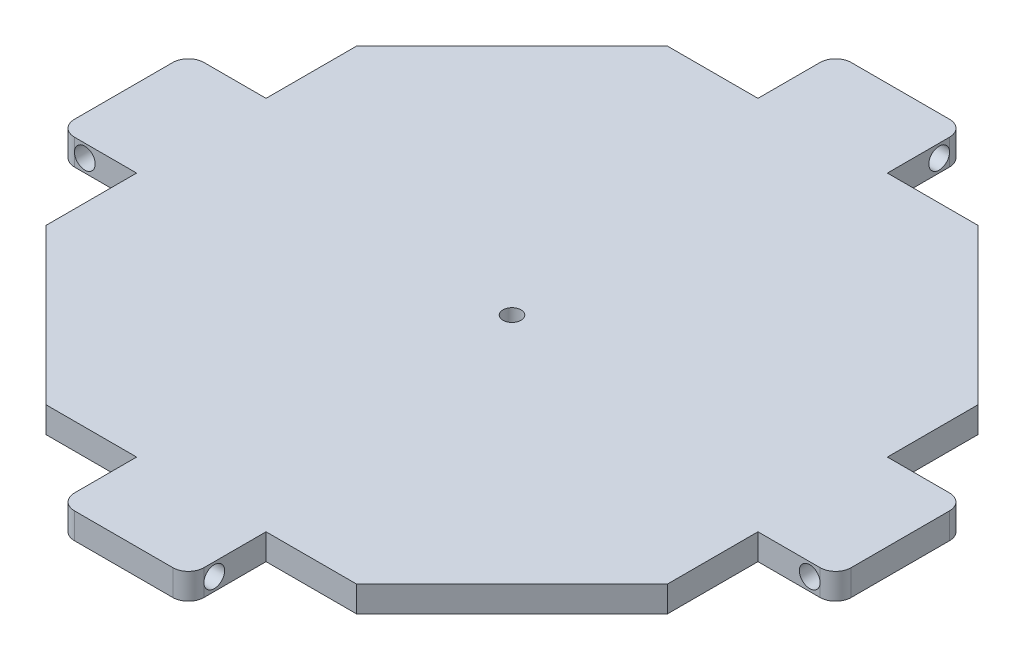
SolidWorks part; units mm, degrees
material "6061 합금"
ref_plane "정면" through (0, 0, 0) normal (0, 0, 1) x (1, 0, 0)
ref_plane "윗면" through (0, 0, 0) normal (0, 1, 0) x (1, 0, 0)
ref_plane "우측면" through (0, 0, 0) normal (1, 0, 0) x (0, 0, -1)
sketch "스케치1" plane through (0, 0, 0) normal (0, 1, 0) x (1, 0, 0)
  line L0 (0, 0) -> (-27.1519, 0) construction
  line L7 (39, 0) -> (-66.3, 0) construction
  line L9 (0, 39) -> (0, -39) construction
  line L14 (-30, -60) -> (30, -60)
  line L15 (30, -60) -> (60, -30)
  line L16 (60, -30) -> (60, 30)
  line L17 (60, 30) -> (30, 60)
  line L18 (30, 60) -> (-30, 60)
  line L19 (-30, 60) -> (-60, 30)
  line L20 (-60, 30) -> (-60, -30)
  line L21 (-60, -30) -> (-30, -60)
  line L22 (-60, 12.5) -> (-75, 12.5)
  line L23 (-75, 12.5) -> (-75, -12.5)
  line L24 (-75, -12.5) -> (-60, -12.5)
  line L25 (-12.5, -60) -> (-12.5, -75)
  line L26 (-12.5, -75) -> (12.5, -75)
  line L27 (12.5, -75) -> (12.5, -60)
  line L28 (60, -12.5) -> (75, -12.5)
  line L29 (75, -12.5) -> (75, 12.5)
  line L30 (75, 12.5) -> (60, 12.5)
  line L31 (-12.5, 60) -> (-12.5, 75)
  line L32 (-12.5, 75) -> (12.5, 75)
  line L33 (12.5, 75) -> (12.5, 60)
  point P0 (0, 0)
  dimension "D3" = 60
  dimension "D4" = 60
  dimension "D5" = 60
  dimension "D6" = 60
  dimension "D7" = 30
  dimension "D8" = 30
  dimension "D9" = 30
  dimension "D10" = 30
  dimension "D11" = 30
  dimension "D12" = 30
  dimension "D13" = 30
  dimension "D15" = 25
  dimension "D16" = 25
  dimension "D17" = 25
  dimension "D18" = 25
  dimension "D19" = 15
  dimension "D21" = 15
  dimension "D22" = 15
  dimension "D23" = 15
  dimension "D24" = 12.5
  dimension "D25" = 12.5
  dimension "D26" = 12.5
extrude "보스-돌출1" add sketch "스케치1" along normal blind 5
fillet "필렛1" radius 3 8 edges at (-12.5, 2.5, 75) (75, 2.5, 12.5) (75, 2.5, -12.5) (12.5, 2.5, -75) (-12.5, 2.5, -75) (-75, 2.5, -12.5) (-75, 2.5, 12.5) (12.5, 2.5, 75)
sketch "스케치7" plane through (0, 5, 0) normal (0, 1, 0) x (1, 0, 0)
  circle A0 centre (0, 0) radius 1.75
  dimension "D1" = 3.5
extrude "컷-돌출5" cut sketch "스케치7" against normal through all
sketch "스케치11" plane through (0, 0, 12.5) normal (0, 0, 1) x (1, 0, 0)
  line L0 (-75, 0) -> (-75, 5) construction
  line L1 (-72, 5) -> (-60, 5) construction
  line L2 (75, 5) -> (75, 0) construction
  line L3 (60, 5) -> (72, 5) construction
  circle A0 centre (-70, 2.5) radius 2
  circle A1 centre (70, 2.5) radius 2
  dimension "D1" = 4
  dimension "D6" = 4
  dimension "D2" = 5
  dimension "D3" = 2.5
  dimension "D4" = 5
  dimension "D5" = 2.5
extrude "컷-돌출6" cut sketch "스케치11" against normal through all
sketch "스케치12" plane through (-12.5, 0, 0) normal (-1, 0, 0) x (0, 0, 1)
  line L0 (-75, 0) -> (-75, 5) construction
  line L1 (-60, 5) -> (-72, 5) construction
  line L2 (75, 5) -> (75, 0) construction
  circle A0 centre (-70, 2.5) radius 2
  circle A1 centre (70, 2.5) radius 2
  dimension "D3" = 4
  dimension "D4" = 4
  dimension "D1" = 5
  dimension "D2" = 2.5
  dimension "D5" = 5
extrude "컷-돌출7" cut sketch "스케치12" against normal through all
